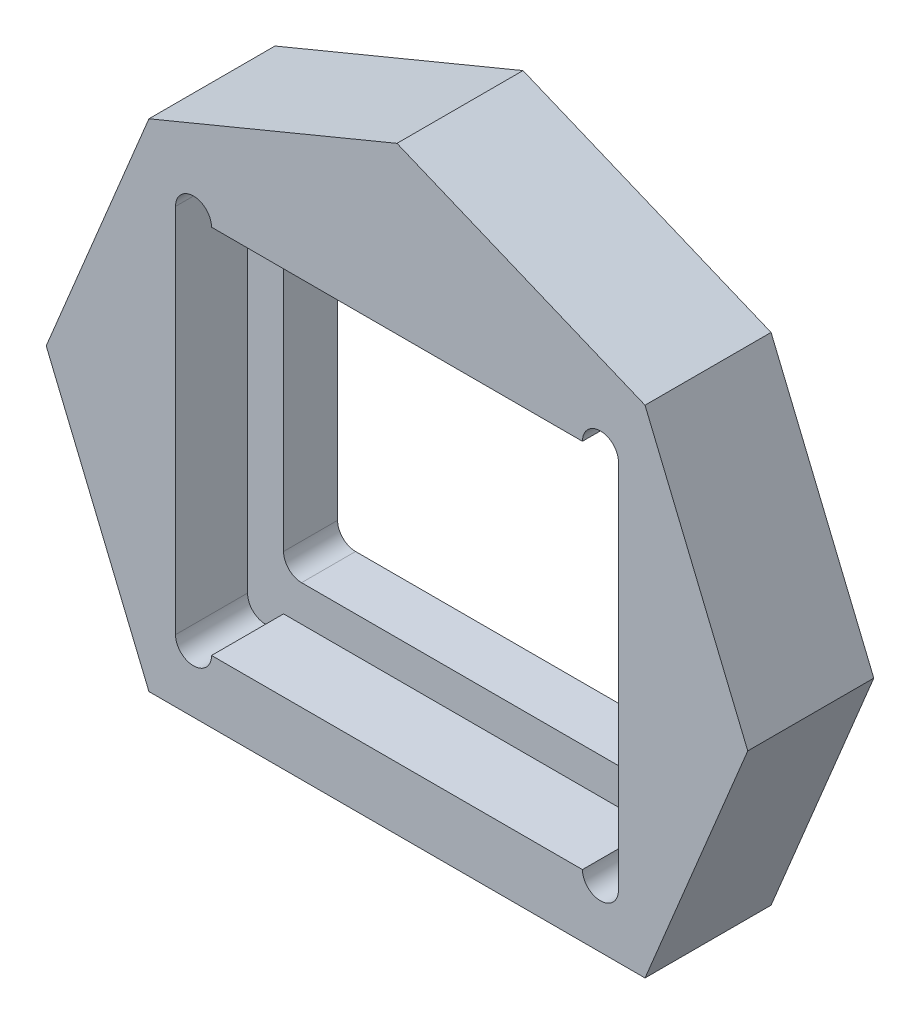
SolidWorks part; units mm, degrees
ref_plane "Front Plane" through (0, 0, 0) normal (0, 0, 1) x (1, 0, 0)
ref_plane "Top Plane" through (0, 0, 0) normal (0, 1, 0) x (1, 0, 0)
ref_plane "Right Plane" through (0, 0, 0) normal (1, 0, 0) x (0, 0, -1)
sketch "Sketch1" plane through (0, 0, 0) normal (0, 0, 1) x (1, 0, 0)
  line L0 (-5.15, -3.65) -> (-5.15, 3.65)
  line L1 (-6, -5) -> (6, -5) construction
  line L2 (-6, -5) -> (-6, 5) construction
  line L3 (-6, 5) -> (6, 5) construction
  line L4 (6, -5) -> (6, 5) construction
  line L5 (-6, -5) -> (6, 5) construction
  line L6 (-6, 5) -> (6, -5) construction
  line L7 (-4.65, 4.15) -> (4.65, 4.15)
  line L8 (5.15, -3.65) -> (5.15, 3.65)
  line L9 (-4.65, -4.15) -> (4.65, -4.15)
  line L10 (-5.15, -4.15) -> (-5.15, 4.15) construction
  line L11 (-5.15, -4.15) -> (5.15, -4.15) construction
  line L12 (5.15, -4.15) -> (5.15, 4.15) construction
  line L13 (-5.15, 4.15) -> (5.15, 4.15) construction
  line L19 (6.8883, 6.8883) -> (0, 9.7415)
  line L20 (0, 9.7415) -> (-6.8883, 6.8883)
  line L21 (-6.8883, 6.8883) -> (-9.7415, 0)
  line L22 (-9.7415, 0) -> (-6.8883, -6.8883)
  line L23 (-6.8883, -6.8883) -> (0, -9.7415)
  line L24 (0, -9.7415) -> (6.8883, -6.8883)
  line L25 (6.8883, -6.8883) -> (9.7415, 0)
  line L26 (9.7415, 0) -> (6.8883, 6.8883)
  arc A0 (-5.15, -3.65) -> (-4.65, -4.15) centre (-4.65, -3.65) ccw
  arc A1 (5.15, -3.65) -> (4.65, -4.15) centre (4.65, -3.65) cw
  arc A2 (4.65, 4.15) -> (5.15, 3.65) centre (4.65, 3.65) cw
  arc A3 (-5.15, 3.65) -> (-4.65, 4.15) centre (-4.65, 3.65) cw
  circle A4 centre (0, 0) radius 9 construction
  point P0 (0, 0)
  dimension "D4" = 0.5
  dimension "D5" = 18
  dimension "D1" = 12
  dimension "D2" = 10
  dimension "D3" = 0.85
extrude "Boss-Extrude1" add sketch "Sketch1" along normal blind 1.5
sketch "Sketch2" plane through (0, 0, 1.5) normal (0, 0, 1) x (1, 0, 0)
  line L3 (-6.15, -5.15) -> (6.15, -5.15)
  line L4 (-6.15, -5.15) -> (-6.15, 5.15)
  line L5 (-6.15, 5.15) -> (6.15, 5.15)
  line L6 (6.15, -5.15) -> (6.15, 5.15)
  line L7 (-6.15, -5.15) -> (6.15, 5.15) construction
  line L8 (9.7415, 0) -> (6.8883, 6.8883)
  line L9 (6.8883, 6.8883) -> (0, 9.7415)
  line L10 (0, 9.7415) -> (-6.8883, 6.8883)
  line L11 (-6.8883, 6.8883) -> (-9.7415, 0)
  line L12 (-9.7415, 0) -> (-6.8883, -6.8883)
  line L13 (-6.8883, -6.8883) -> (0, -9.7415)
  line L14 (0, -9.7415) -> (6.8883, -6.8883)
  line L15 (6.8883, -6.8883) -> (9.7415, 0)
  line L16 (9.7415, 0) -> (6.8883, 6.8883)
  line L17 (6.8883, 6.8883) -> (0, 9.7415)
  line L18 (0, 9.7415) -> (-6.8883, 6.8883)
  line L19 (-6.8883, 6.8883) -> (-9.7415, 0)
  line L20 (-9.7415, 0) -> (-6.8883, -6.8883)
  line L21 (-6.8883, -6.8883) -> (0, -9.7415)
  line L22 (0, -9.7415) -> (6.8883, -6.8883)
  line L23 (6.8883, -6.8883) -> (9.7415, 0)
  line L24 (-6.15, 5.15) -> (6.15, -5.15) construction
  point P18 (0, 0)
  dimension "D2" = 12.3
  dimension "D3" = 10.3
  dimension "D1" = 0
extrude "Boss-Extrude2" add sketch "Sketch2" along normal blind 2
sketch "Sketch3" plane through (0, 0, 3.5) normal (0, 0, 1) x (1, 0, 0)
  line L0 (-5.65, -5.15) -> (-5.65, 5.15) construction
  line L1 (-6.15, -5.15) -> (-6.15, 5.15)
  line L2 (-5.15, -5.15) -> (-5.15, 5.15)
  line L3 (5.65, -5.15) -> (5.65, 5.15) construction
  line L4 (5.15, -5.15) -> (5.15, 5.15)
  line L5 (6.15, -5.15) -> (6.15, 5.15)
  line L6 (6.15, -5.15) -> (6.15, 5.15) construction
  line L7 (-6.15, 5.15) -> (-6.15, -5.15) construction
  line L8 (6.15, 5.15) -> (-6.15, 5.15) construction
  line L9 (-6.15, -5.15) -> (6.15, -5.15) construction
  line L10 (-6.15, -5.15) -> (6.15, -5.15) construction
  arc A0 (-6.15, -5.15) -> (-5.15, -5.15) centre (-5.65, -5.15) ccw
  arc A1 (-5.15, 5.15) -> (-6.15, 5.15) centre (-5.65, 5.15) ccw
  arc A2 (5.15, -5.15) -> (6.15, -5.15) centre (5.65, -5.15) ccw
  arc A3 (6.15, 5.15) -> (5.15, 5.15) centre (5.65, 5.15) ccw
  point P2 (-5.65, 0)
  point P8 (5.65, 0)
  dimension "D1" = 1
extrude "Cut-Extrude1" cut sketch "Sketch3" against normal up to surface (2 mm away) up to face at (0, 0, 1.5)
sketch "Sketch4" plane through (0, 0, 3.5) normal (0, 0, 1) x (1, 0, 0)
  line L0 (-6.8883, -6.8883) -> (6.8883, -6.8883)
  line L1 (6.8883, -6.8883) -> (0, -9.7415)
  line L2 (0, -9.7415) -> (-6.8883, -6.8883)
extrude "Cut-Extrude2" cut sketch "Sketch4" against normal up to next
